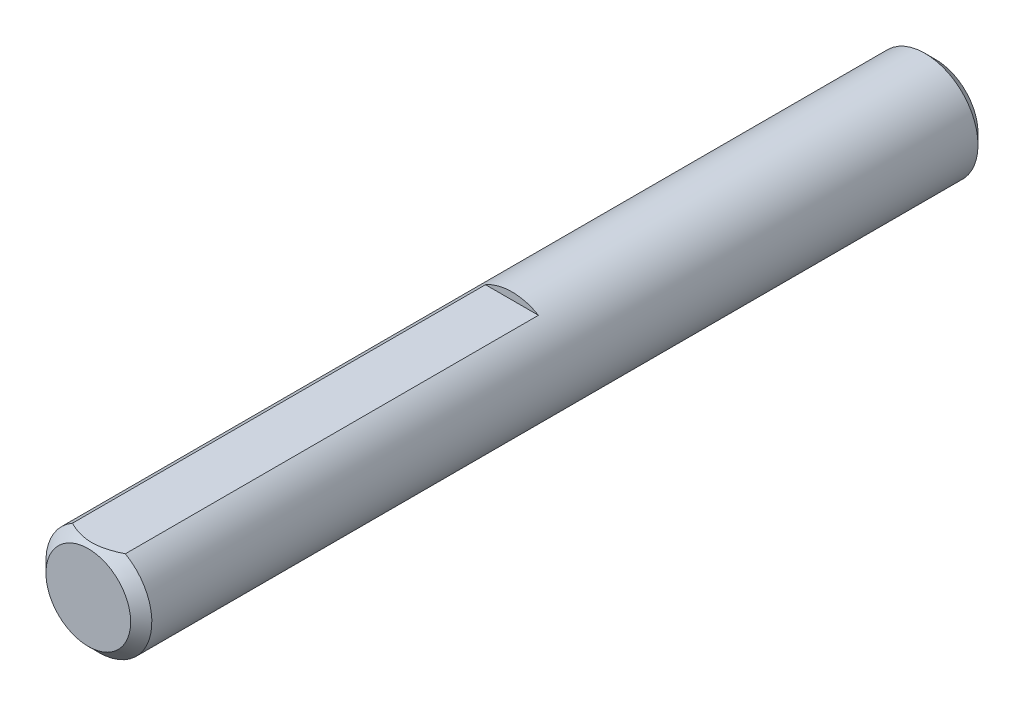
SolidWorks part; units mm, degrees
ref_plane "Front" through (0, 0, 0) normal (0, 0, 1) x (1, 0, 0)
ref_plane "Top" through (0, 0, 0) normal (0, 1, 0) x (1, 0, 0)
ref_plane "Right" through (0, 0, 0) normal (1, 0, 0) x (0, 0, -1)
sketch "Sketch1" plane through (0, 0, 0) normal (0, 0, 1) x (1, 0, 0)
  circle A0 centre (0, 0) radius 3.175
  dimension "D1" = 6.35
extrude "Extrude1" add sketch "Sketch1" along normal mid plane 50.8
chamfer "Chamfer1" distance 0.635 angle 45 2 edges at (3.175, 0, -25.4) (3.175, 0, 25.4)
ref_plane "Plane1" through (0, 0, 0) normal (0, 0, 1) x (1, 0, 0)
sketch "Sketch13" plane through (0, 0, 0) normal (0, 0, 1) x (1, 0, 0)
  line L3 (-1.5875, 2.7496) -> (1.5875, 2.7496)
  circle A0 centre (0, 0) radius 3.175 construction
  arc A1 (1.5875, 2.7496) -> (-1.5875, 2.7496) centre (0, 0) ccw
  dimension "D1" = 3.175
extrude "Extrude7" cut sketch "Sketch13" along normal through all
equation "\"D1@Chamfer1\" = \"D1@Sketch1\" * .1"
equation "\"D1@Sketch13\" = \"D1@Sketch1\" * .5"
